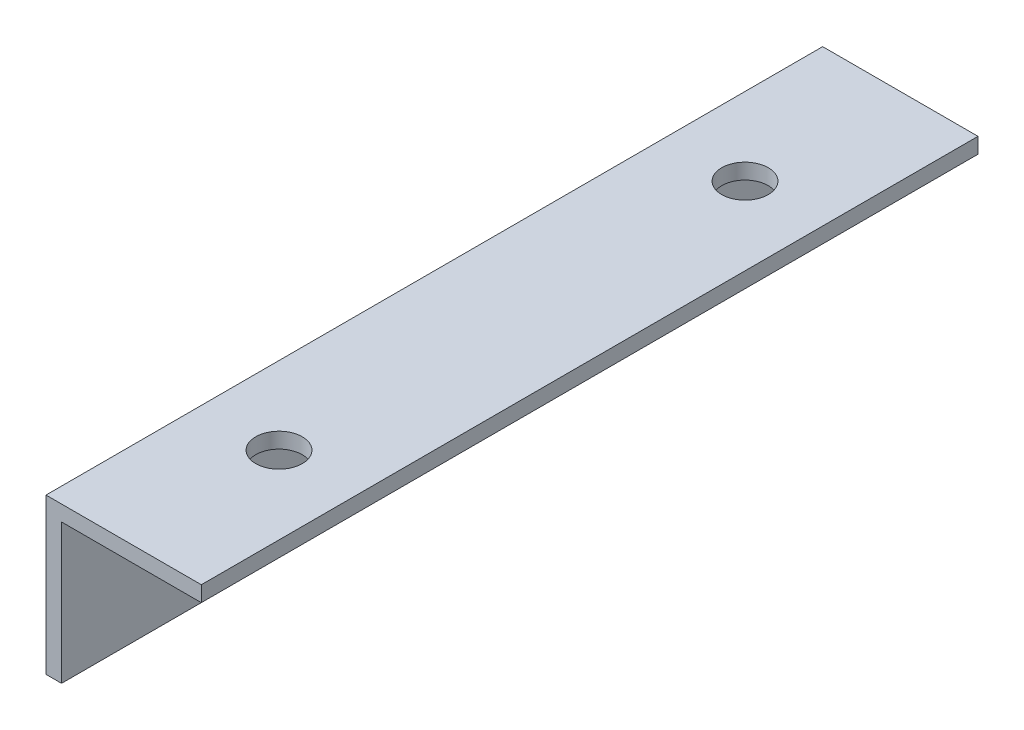
SolidWorks part; units mm, degrees
ref_plane "Front Plane" through (0, 0, 0) normal (0, 0, 1) x (1, 0, 0)
ref_plane "Top Plane" through (0, 0, 0) normal (0, 1, 0) x (1, 0, 0)
ref_plane "Right Plane" through (0, 0, 0) normal (1, 0, 0) x (0, 0, -1)
sketch "Sketch2" plane through (0, 0, 0) normal (0, 0, 1) x (1, 0, 0)
  line L0 (0, 0) -> (0, 20)
  line L1 (0, 20) -> (20, 20)
  line L2 (0, 0) -> (2, 0)
  line L3 (20, 20) -> (20, 18)
  line L4 (20, 18) -> (2, 18)
  line L5 (2, 18) -> (2, 0)
  dimension "D1" = 20
  dimension "D2" = 20
  dimension "D3" = 2
  dimension "D4" = 2
extrude "Boss-Extrude1" add sketch "Sketch2" along normal blind 100
sketch "Sketch3" plane through (0, 0, 0) normal (-1, 0, 0) x (0, 0, 1)
  line L0 (100, 10) -> (80, 10) construction
  line L1 (100, 20) -> (100, 0) construction
  circle A0 centre (80, 10) radius 3
  dimension "D1" = 20
extrude "Cut-Extrude1" cut sketch "Sketch3" against normal blind 20
sketch "Sketch4" plane through (0, 0, 0) normal (-1, 0, 0) x (0, 0, 1)
  line L0 (0, 10) -> (20, 10) construction
  line L1 (0, 20) -> (0, 0) construction
  circle A0 centre (20, 10) radius 3
  dimension "D1" = 20
extrude "Cut-Extrude2" cut sketch "Sketch4" against normal blind 20
sketch "Sketch5" plane through (0, 20, 0) normal (0, 1, 0) x (1, 0, 0)
  line L0 (0, -100) -> (10, -100) construction
  line L1 (20, -100) -> (0, -100) construction
  line L2 (10, -100) -> (10, -80) construction
  circle A0 centre (10, -80) radius 3
  dimension "D1" = 20
extrude "Cut-Extrude3" cut sketch "Sketch5" against normal blind 20
sketch "Sketch6" plane through (0, 20, 0) normal (0, 1, 0) x (1, 0, 0)
  line L0 (0, 0) -> (10, 0) construction
  line L1 (20, 0) -> (0, 0) construction
  line L2 (10, 0) -> (10, -20) construction
  circle A0 centre (10, -20) radius 3
  dimension "D1" = 20
extrude "Cut-Extrude4" cut sketch "Sketch6" against normal blind 20
